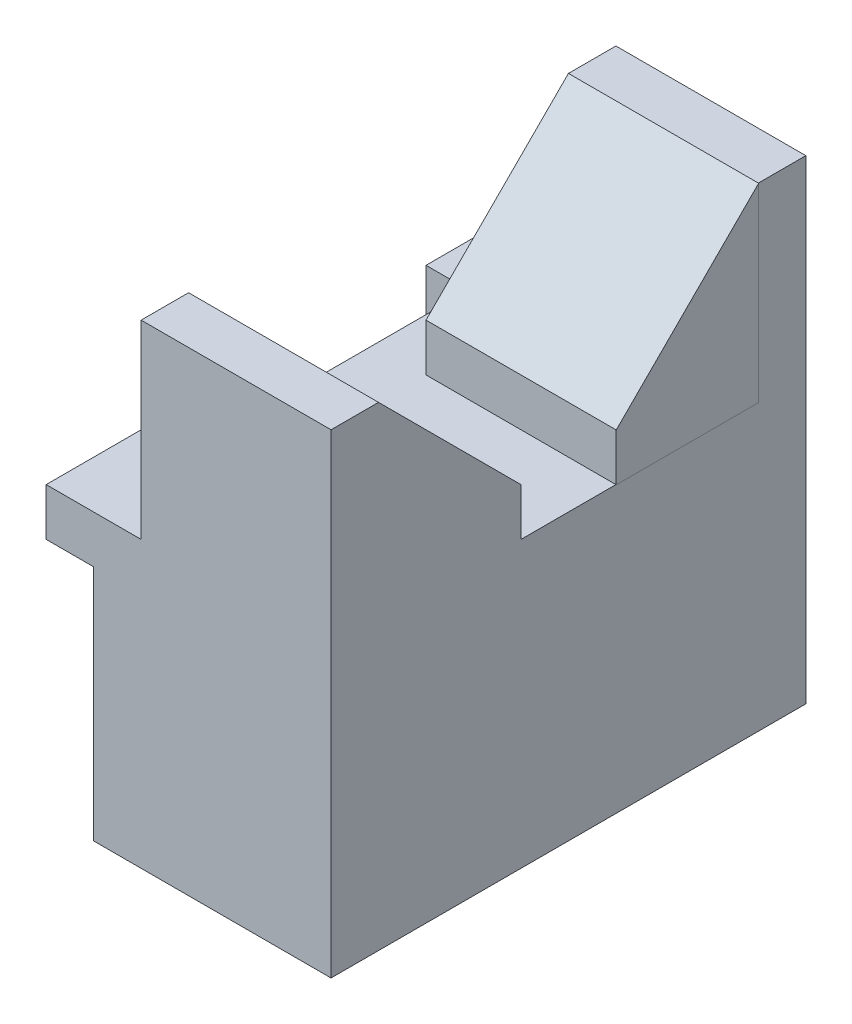
SolidWorks part; units mm, degrees
ref_plane "Front Plane" through (0, 0, 0) normal (0, 0, 1) x (1, 0, 0)
ref_plane "Top Plane" through (0, 0, 0) normal (0, 1, 0) x (1, 0, 0)
ref_plane "Right Plane" through (0, 0, 0) normal (1, 0, 0) x (0, 0, -1)
sketch "Sketch1" plane through (0, 0, 0) normal (0, 1, 0) x (1, 0, 0)
  line L1 (0, 0) -> (25, 0)
  line L2 (0, 0) -> (0, -50)
  line L3 (0, -50) -> (25, -50)
  line L4 (25, 0) -> (25, -50)
  dimension "D1" = 50
  dimension "D2" = 25
extrude "Boss-Extrude1" add sketch "Sketch1" along normal blind 25
ref_plane "Plane1" through (0, 25, 0) normal (0, 1, 0) x (1, 0, 0)
sketch "Sketch2" plane through (0, 25, 0) normal (0, 1, 0) x (1, 0, 0)
  line L0 (0, 0) -> (-5, 0)
  line L1 (-5, 0) -> (-5, -10)
  line L2 (-5, -10) -> (0, -10)
  line L3 (0, 0) -> (0, -50) construction
  line L4 (0, 0) -> (0, -10)
  dimension "D2" = 10
extrude "Boss-Extrude2" add sketch "Sketch2" along normal blind 5 separate body
sketch "Sketch3" plane through (0, 25, 0) normal (0, 1, 0) x (1, 0, 0)
  line L1 (0, 0) -> (25, 0)
  line L2 (0, 0) -> (0, -50)
  line L3 (0, -50) -> (25, -50)
  line L4 (25, 0) -> (25, -50)
extrude "Boss-Extrude3" add sketch "Sketch3" along normal blind 5
sketch "Sketch4" plane through (0, 30, 0) normal (0, 1, 0) x (1, 0, 0)
  line L1 (0, -50) -> (-5, -50)
  line L2 (0, -50) -> (0, -40)
  line L3 (0, -40) -> (-5, -40)
  line L4 (-5, -50) -> (-5, -40)
  dimension "D1" = 10
  dimension "D2" = 5
extrude "Boss-Extrude5" add sketch "Sketch4" against normal blind 5
ref_plane "Plane2" through (0, 0, 0) normal (-1, 0, 0) x (0, 0, 1)
sketch "Sketch6" plane through (0, 0, 0) normal (-1, 0, 0) x (0, 0, 1)
  line L0 (55, 25) -> (-55, 25) construction
  line L1 (10, 30) -> (40.0479, 30)
  line L2 (10, 30) -> (10, 25)
  line L3 (10, 25) -> (40.0479, 25)
  line L4 (40.0479, 30) -> (40.0479, 25)
extrude "Boss-Extrude6" add sketch "Sketch6" along normal blind 0.5
ref_plane "Plane3" through (0, 30, 0) normal (0, 1, 0) x (1, 0, 0)
sketch "Sketch8" plane through (0, 30, 0) normal (0, 1, 0) x (1, 0, 0)
  line L0 (-5, 0) -> (5, 0) construction
  line L1 (25, 0) -> (-5, 0) construction
  line L3 (25, 0) -> (5, 0)
  line L4 (25, 0) -> (25, -5)
  line L5 (25, -5) -> (5, -5)
  line L6 (5, 0) -> (5, -5)
  dimension "D1" = 10
  dimension "D2" = 20
  dimension "D3" = 5
extrude "Boss-Extrude7" add sketch "Sketch8" along normal blind 20
ref_plane "Plane4" through (5, 30, 0) normal (-1, 0, 0) x (0, 0, 1)
sketch "Sketch12" plane through (0, 30, 0) normal (0, 1, 0) x (1, 0, 0)
  line L0 (25, -5) -> (25, -25) construction
  line L1 (25, -50) -> (25, -5) construction
  line L2 (25, -5) -> (25, 0) construction
  point P4 (25, -23.6145)
  point P5 (25, -5)
  point P8 (25, -26.1954)
  point P9 (25, -26.1954)
  dimension "D1" = 20
sketch "Sketch15" plane through (0, 30, 0) normal (0, 1, 0) x (1, 0, 0)
  line L5 (5, -5) -> (25.0346, -5)
  line L6 (5, -5) -> (5, -20)
  line L7 (5, -20) -> (25.0346, -20)
  line L8 (25.0346, -5) -> (25.0346, -20)
  line L9 (25, -50) -> (5, -50)
  line L10 (25, -50) -> (25, -30)
  line L11 (25, -30) -> (5, -30)
  line L12 (5, -50) -> (5, -30)
  dimension "D1" = 15
  dimension "D2" = 20
  dimension "D3" = 20
sketch "Sketch18" plane through (0, 30, 0) normal (0, 1, 0) x (1, 0, 0)
  line L0 (25, -25) -> (25, -35) construction
  line L1 (25, -50) -> (25, -5) construction
  line L2 (-5, -50) -> (25, -50) construction
  line L3 (25, -35) -> (5, -35)
  line L4 (25, -35) -> (25, -50)
  line L5 (25, -50) -> (5, -50)
  line L6 (5, -35) -> (5, -50)
  dimension "D1" = 10
  dimension "D2" = 20
extrude "Boss-Extrude9" add sketch "Sketch18" along normal blind 20
sketch "Sketch20" plane through (5, 0, 0) normal (-1, 0, 0) x (0, 0, 1)
  line L1 (35, 50) -> (50, 50) construction
  line L2 (35, 30) -> (35, 35) construction
  line L3 (35, 50) -> (35, 30) construction
  line L4 (45, 50) -> (35, 35)
  line L5 (35, 35) -> (35, 50)
  line L6 (35, 50) -> (45, 50)
  point P10 (0, 0)
  dimension "D2" = 5
extrude "Cut-Extrude7" cut sketch "Sketch20" against normal blind 20
extrude "Boss-Extrude11" add sketch "Sketch15" along normal blind 20
sketch "Sketch21" plane through (5, 0, 0) normal (-1, 0, 0) x (0, 0, 1)
  line L0 (20, 30) -> (20, 35) construction
  line L1 (20, 50) -> (20, 30) construction
  line L2 (30, 30) -> (30, 35) construction
  line L3 (30, 50) -> (30, 30) construction
  line L4 (0, 50) -> (5, 50) construction
  line L5 (0, 50) -> (20, 50) construction
  line L6 (50, 50) -> (45, 50) construction
  line L7 (30, 50) -> (50, 50) construction
  line L8 (5, 50) -> (20, 50)
  line L9 (20, 50) -> (20, 35)
  line L10 (20, 35) -> (5, 50)
  line L11 (45, 50) -> (30, 35)
  line L12 (30, 35) -> (30, 50)
  line L13 (30, 50) -> (45, 50)
  dimension "D1" = 5
  dimension "D2" = 5
  dimension "D3" = 5
  dimension "D4" = 5
extrude "Cut-Extrude9" cut sketch "Sketch21" against normal blind 30
